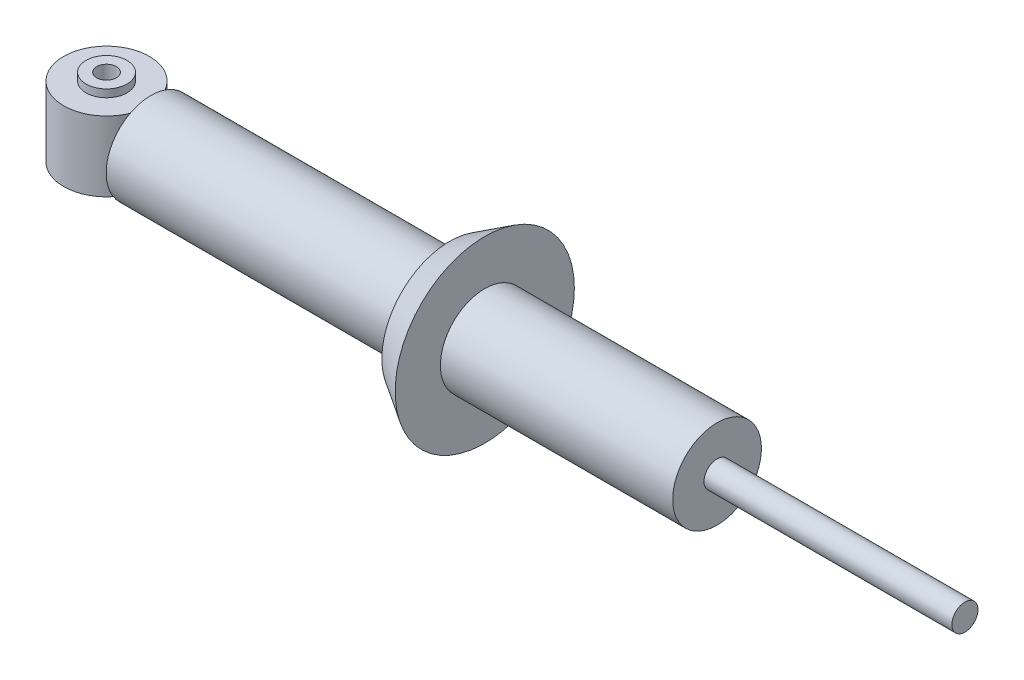
SolidWorks part; units mm, degrees
ref_plane "前视基准面" through (0, 0, 0) normal (0, 0, 1) x (1, 0, 0)
ref_plane "上视基准面" through (0, 0, 0) normal (0, 1, 0) x (1, 0, 0)
ref_plane "右视基准面" through (0, 0, 0) normal (1, 0, 0) x (0, 0, -1)
sketch "草图1" plane through (0, 0, 0) normal (0, 0, 1) x (1, 0, 0)
  line L0 (-61.4376, 0) -> (64.7686, 0) construction
  line L1 (0, 58.9394) -> (0, -65.6013) construction
  line L2 (-5.75, 25) -> (-12, 25)
  line L3 (-12, 25) -> (-12, 20.5)
  line L4 (-12, 20.5) -> (-25.1, 20.5)
  line L5 (-25.1, 20.5) -> (-25.1, -20.5)
  line L6 (-5.75, 25) -> (-5.75, -25)
  line L7 (-5.75, -25) -> (-12, -25)
  line L8 (-12, -25) -> (-12, -20.5)
  line L9 (-12, -20.5) -> (-25.1, -20.5)
  point P12 (-5.75, 0)
  point P15 (-25.1, 0)
  dimension "D1" = 5.75
  dimension "D2" = 12
  dimension "D3" = 20.5
  dimension "D4" = 4.5
  dimension "D5" = 25.1
revolve "旋转1" add sketch "草图1" angle 360 about L1
ref_plane "基准面1" through (201, 0, 0) normal (1, 0, 0) x (0, 0, -1)
sketch "草图2" plane through (201, 0, 0) normal (1, 0, 0) x (0, 0, -1)
  circle A0 centre (0, 0) radius 26.2
  dimension "D1" = 52.4
extrude "凸台-拉伸1" add sketch "草图2" against normal blind 175
ref_plane "基准面2" through (26, 0, 0) normal (1, 0, 0) x (0, 0, -1)
sketch "草图3" plane through (26, 0, 0) normal (1, 0, 0) x (0, 0, -1)
  line L0 (-13.4765, 0) -> (13.4765, 0) construction
  line L1 (0, 14.4691) -> (0, -15.0708) construction
  line L2 (10, 10) -> (10, -10)
  line L3 (10, -10) -> (-10, -10)
  line L4 (-10, -10) -> (-10, 10)
  line L5 (-10, 10) -> (10, 10)
  dimension "D1" = 20
  dimension "D2" = 20
  dimension "D3" = 10
  dimension "D4" = 10
extrude "凸台-拉伸2" add sketch "草图3" against normal blind 3
sketch "草图4" plane through (201, 0, 0) normal (1, 0, 0) x (0, 0, -1)
  circle A0 centre (0, 0) radius 39.7
ref_plane "基准面3" through (221.6, 0, 0) normal (1, 0, 0) x (0, 0, -1)
sketch "草图5" plane through (221.6, 0, 0) normal (1, 0, 0) x (0, 0, -1)
  circle A0 centre (0, 0) radius 52.5
  dimension "D1" = 105
loft "放样2" add profiles "草图4", "草图5"
sketch "草图6" plane through (221.6, 0, 0) normal (1, 0, 0) x (0, 0, -1)
  circle A0 centre (0, 0) radius 26
  dimension "D1" = 52
extrude "凸台-拉伸3" add sketch "草图6" along normal blind 136.1
sketch "草图7" plane through (357.7, 0, 0) normal (1, 0, 0) x (0, 0, -1)
  circle A0 centre (0, 0) radius 7.65
  dimension "D1" = 15.3
extrude "凸台-拉伸4" add sketch "草图7" along normal blind 145.23
